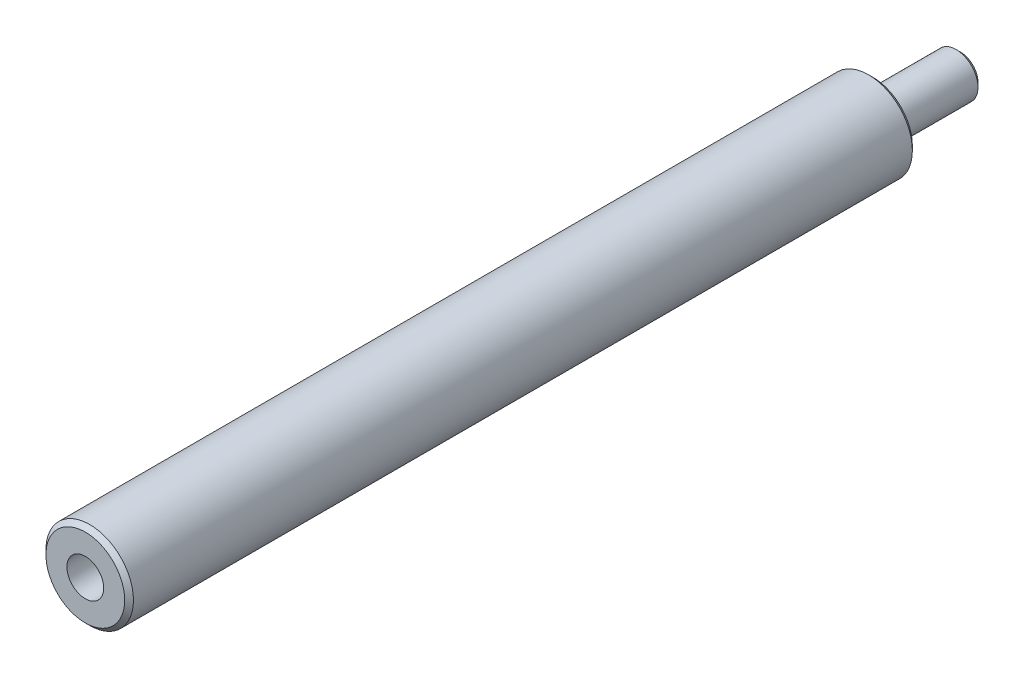
SolidWorks part; units mm, degrees
material "Alumine"
ref_plane "Plan de face" through (0, 0, 0) normal (0, 0, 1) x (1, 0, 0)
ref_plane "Plan de dessus" through (0, 0, 0) normal (0, 1, 0) x (1, 0, 0)
ref_plane "Plan de droite" through (0, 0, 0) normal (1, 0, 0) x (0, 0, -1)
sketch "Esquisse1" plane through (0, 0, 0) normal (0, 0, 1) x (1, 0, 0)
  circle A0 centre (0, 0) radius 5
  dimension "D1" = 10
extrude "Boss.-Extru.1" add sketch "Esquisse1" along normal blind 90
sketch "Esquisse2" plane through (0, 0, 0) normal (0, 0, -1) x (-1, 0, 0)
  circle A0 centre (0, 0) radius 2.5
  dimension "D1" = 5
extrude "Boss.-Extru.2" add sketch "Esquisse2" along normal blind 10
hole_wizard "Trou pour taraudage pour trou taraudé M51" positions "Esquisse3" profile "Esquisse4" hole size "M5" standard "ISO"
sketch "Esquisse3" plane through (0, 0, 90) normal (0, 0, 1) x (1, 0, 0)
  point P0 (0, 0)
sketch "Esquisse4" plane through (0, 0, 90) normal (1, 0, 0) x (0, -1, 0)
  line L0 (0, 0) -> (0, 11.2618)
  line L1 (0, 11.2618) -> (2.1, 10)
  line L2 (2.1, 10) -> (2.1, 0)
  line L5 (2.1, 0) -> (0, 0)
  line L10 (0, 11.2618) -> (-2.1, 10) construction
  line L11 (0, -6.35) -> (0, 107.95) construction
  dimension "Diamètre du perçage" = 4.2
  dimension "Profondeur du perçage" = 10
  dimension "Angle de pointe" = 118
chamfer "Chanfrein1" distance 0.5 angle 45 3 edges at (5, 0, 0) (5, 0, 90) (-2.5, 0, -10)
